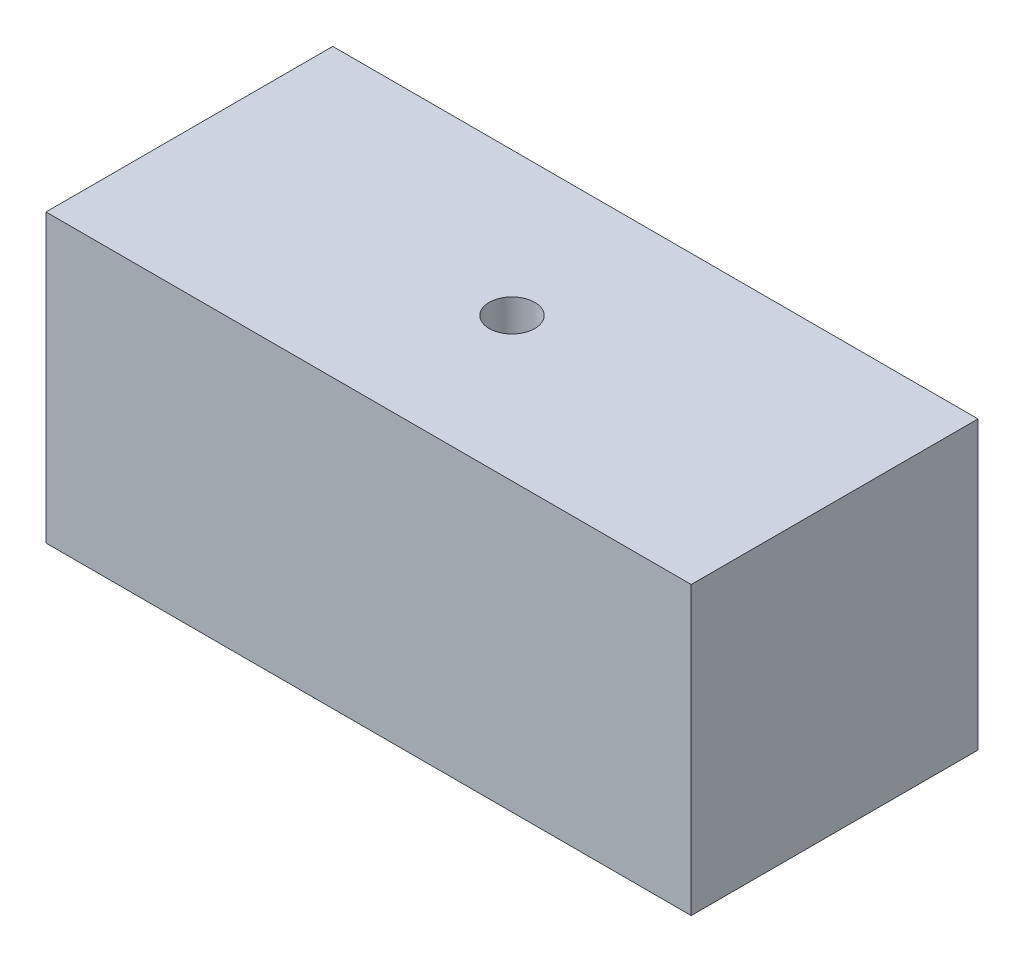
SolidWorks part; units mm, degrees
ref_plane "Front Plane" through (0, 0, 0) normal (0, 0, 1) x (1, 0, 0)
ref_plane "Top Plane" through (0, 0, 0) normal (0, 1, 0) x (1, 0, 0)
ref_plane "Right Plane" through (0, 0, 0) normal (1, 0, 0) x (0, 0, -1)
sketch "Sketch1" plane through (0, 0, 0) normal (0, 1, 0) x (1, 0, 0)
  line L1 (-45, 20) -> (45, 20)
  line L2 (-45, 20) -> (-45, -20)
  line L3 (-45, -20) -> (45, -20)
  line L4 (45, 20) -> (45, -20)
  line L5 (-45, 20) -> (45, -20) construction
  line L6 (-45, -20) -> (45, 20) construction
  point P0 (0, 0)
  dimension "D1" = 90
  dimension "D2" = 40
extrude "Boss-Extrude1" add sketch "Sketch1" along normal blind 40
sketch "Sketch2" plane through (0, 0, -20) normal (0, 0, -1) x (-1, 0, 0)
  line L0 (-45, 20) -> (45, 20) construction
  line L1 (-45, 40) -> (-45, 0) construction
  line L2 (45, 40) -> (45, 0) construction
  circle A0 centre (-25, 20) radius 10
  dimension "D2" = 20
  dimension "D1" = 20
extrude "Boss-Extrude2" add sketch "Sketch2" along normal blind 5
sketch "Sketch3" plane through (0, 40, 0) normal (0, 1, 0) x (1, 0, 0)
  line L0 (45, 0) -> (-45, 0) construction
  line L1 (45, -20) -> (45, 20) construction
  line L2 (-45, 20) -> (-45, -20) construction
  circle A0 centre (0, 0) radius 3.175
  dimension "D1" = 6.35
  dimension "D2" = 45
extrude "Cut-Extrude1" cut sketch "Sketch3" against normal through all
